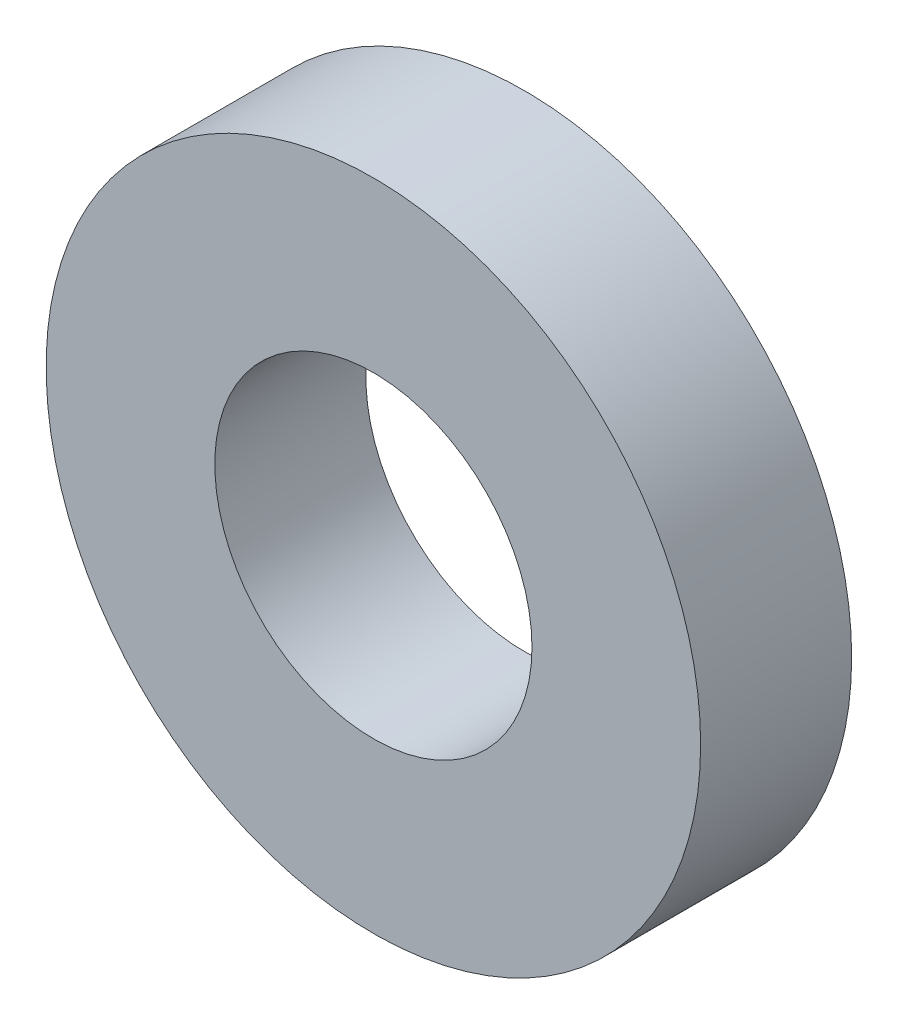
SolidWorks part; units mm, degrees
ref_plane "Front Plane" through (0, 0, 0) normal (0, 0, 1) x (1, 0, 0)
ref_plane "Top Plane" through (0, 0, 0) normal (0, 1, 0) x (1, 0, 0)
ref_plane "Right Plane" through (0, 0, 0) normal (1, 0, 0) x (0, 0, -1)
sketch "Sketch1" plane through (0, 0, 0) normal (0, 0, 1) x (1, 0, 0)
  circle A0 centre (0, 0) radius 6.5
  circle A1 centre (0, 0) radius 3.15
  dimension "OD" = 13
  dimension "ID" = 6.3
extrude "Extrude1" add sketch "Sketch1" along normal mid plane 3
sketch "Sketch2" plane through (0, 0, 0) normal (1, 0, 0) x (0, 0, -1)
  line L0 (-1.5, -3.15) -> (1.5, -3.15) construction
  line L3 (1.5, 3.15) -> (-1.5, 3.15) construction
  line L5 (-1.5, -3.15) -> (1.5, -3.15)
  line L6 (1.5, 3.15) -> (-1.5, 3.15)
sketch "Sketch4" plane through (0, 0, 1.5) normal (0, 0, 1) x (1, 0, 0)
  line L0 (0, 0) -> (-2.2274, 2.2274)
  line L1 (0, -1.1) -> (0, 1.1) construction
  circle A0 centre (0, 0) radius 3.15 construction
  dimension "D1" = 45
